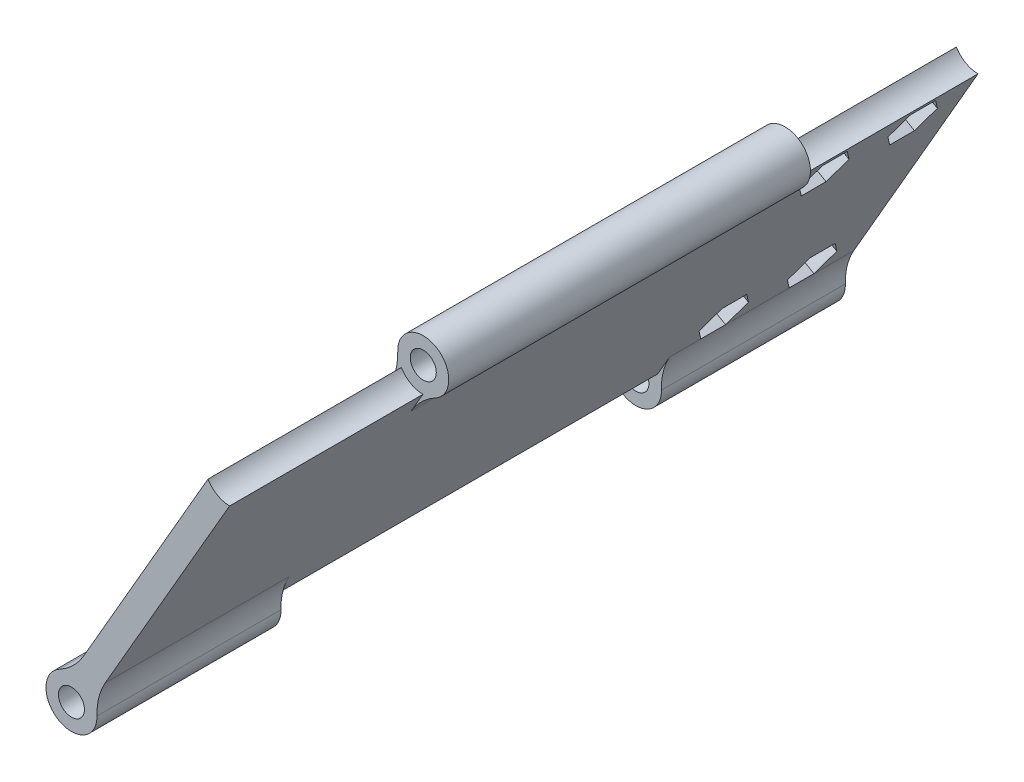
SolidWorks part; units mm, degrees
material "PLA"
ref_plane "Front Plane" through (0, 0, 0) normal (0, 0, 1) x (1, 0, 0)
ref_plane "Top Plane" through (0, 0, 0) normal (0, 1, 0) x (1, 0, 0)
ref_plane "Right Plane" through (0, 0, 0) normal (1, 0, 0) x (0, 0, -1)
sketch "Sketch2" plane through (0, 0, 0) normal (0, 0, 1) x (1, 0, 0)
  line L0 (0, 0) -> (38.1, 0)
  line L1 (0, 0) -> (0, -38.1)
  circle A0 centre (0, 0) radius 38.1
  circle A1 centre (0, -29.337) radius 1.5875
  circle A2 centre (-25.4066, 14.6685) radius 1.5875
  circle A3 centre (25.4066, 14.6685) radius 1.5875
  point P13 (0, 0)
  dimension "D1" = 76.2
  dimension "D2" = 3.175
  dimension "D3" = 8.763
  dimension "D4" = 3
extrude "Boss-Extrude1" add sketch "Sketch2" along normal blind 10 contours A1 L1 L0 A0 A3 A2 | A1 L1 A0 L0
sketch "Sketch3" plane through (0, 0, 10) normal (0, 0, 1) x (1, 0, 0)
  line L1 (0, -29.337) -> (25.4066, 14.6685)
  line L2 (1.7321, -30.337) -> (27.1386, 13.6685)
  line L3 (-1.7321, -28.337) -> (23.6745, 15.6685)
  circle A11 centre (0, -29.337) radius 1.5875
  circle A12 centre (25.4066, 14.6685) radius 1.5875
  circle A17 centre (0, -29.337) radius 2.0875
  circle A18 centre (25.4066, 14.6685) radius 2.0875
  circle A19 centre (0, -29.337) radius 4.0875
  circle A20 centre (25.4066, 14.6685) radius 4.0875
  dimension "D1" = 0.5
  dimension "D2" = 2
  dimension "D4" = 2
  dimension "D5" = 2
extrude "Boss-Extrude2" add sketch "Sketch3" along normal blind 120 separate body contours L2 A20 L3 A18 | L1 A20 L2 A18 | L3 A20 L1 A18 | A20 L1 A19 L2 | A20 L3 A19 L1 | L1 A19 L3 A17 | L2 A19 L1 A17 | L3 A19 L2 A17
delete or keep bodies "Body-Delete/Keep 2" type delete bodies bodies 101
ref_plane "Plane1" through (0, 0, 70) normal (0, 0, 1) x (1, 0, 0)
sketch "Sketch4" plane through (0, 0, 70) normal (0, 0, 1) x (1, 0, 0)
  circle A1 centre (0, -29.337) radius 4.0875
extrude "Cut-Extrude1" cut sketch "Sketch4" against normal blind 30.5 and the other way blind 30.5
sketch "Sketch5" plane through (0, 0, 10) normal (0, 0, -1) x (-1, 0, 0)
  circle A0 centre (-25.4066, 14.6685) radius 4.0875
extrude "Cut-Extrude2" cut sketch "Sketch5" against normal offset from surface (31 mm away) 1.5 up to face at (2.0875, -29.337, 39.5) offset beyond the face yes
sketch "Sketch6" plane through (0, 0, 130) normal (0, 0, 1) x (1, 0, 0)
  circle A0 centre (25.4066, 14.6685) radius 4.0875
extrude "Cut-Extrude3" cut sketch "Sketch6" against normal offset from surface (31 mm away) 1.5 contours A0 up to face at (2.0875, -29.337, 100.5) offset beyond the face yes
fillet "Fillet1" radius 10 6 edges at (21.8921, 12.5813, 70) (0.0503, -25.2498, 24.75) (0.0503, -25.2498, 115.25) (3.5144, -27.2498, 115.25) (3.5144, -27.2498, 24.75) (25.3562, 10.5813, 70)
sketch "Sketch7" plane through (10.9712, -6.3343, 0) normal (-0.866, 0.5, 0) x (0, 0, 1)
  circle A0 centre (18.3842, -14.5821) radius 1.5
  circle A1 centre (32.5542, -14.5821) radius 1.5
  circle A2 centre (18.3842, 17.6479) radius 1.5
  circle A3 centre (32.5542, 17.6479) radius 1.5
extrude "Cut-Extrude4" cut sketch "Sketch7" against normal up to surface (4 mm away) contours A0 | A2 | A3 | A1 up to face at (14.7532, -7.7836, 70)
sketch "Sketch8" plane through (14.4353, -8.3342, 0) normal (0.866, -0.5, 0) x (0, 0, -1)
  line L25 (-28.5948, 17.6686) -> (-30.5924, 21.0872)
  line L26 (-30.5924, 21.0872) -> (-34.5518, 21.0665)
  line L27 (-34.5518, 21.0665) -> (-36.5137, 17.6272)
  line L28 (-36.5137, 17.6272) -> (-34.5161, 14.2086)
  line L29 (-34.5161, 14.2086) -> (-30.5566, 14.2293)
  line L30 (-30.5566, 14.2293) -> (-28.5948, 17.6686)
  line L31 (-14.4248, 17.6686) -> (-16.4224, 21.0872)
  line L32 (-16.4224, 21.0872) -> (-20.3818, 21.0665)
  line L33 (-20.3818, 21.0665) -> (-22.3437, 17.6272)
  line L34 (-22.3437, 17.6272) -> (-20.3461, 14.2086)
  line L35 (-20.3461, 14.2086) -> (-16.3866, 14.2293)
  line L36 (-16.3866, 14.2293) -> (-14.4248, 17.6686)
  line L37 (-14.4248, -14.5614) -> (-16.4224, -11.1428)
  line L38 (-16.4224, -11.1428) -> (-20.3818, -11.1635)
  line L39 (-20.3818, -11.1635) -> (-22.3437, -14.6028)
  line L40 (-22.3437, -14.6028) -> (-20.3461, -18.0214)
  line L41 (-20.3461, -18.0214) -> (-16.3866, -18.0007)
  line L42 (-16.3866, -18.0007) -> (-14.4248, -14.5614)
  line L43 (-28.5948, -14.5614) -> (-30.5924, -11.1428)
  line L44 (-30.5924, -11.1428) -> (-34.5518, -11.1635)
  line L45 (-34.5518, -11.1635) -> (-36.5137, -14.6028)
  line L46 (-36.5137, -14.6028) -> (-34.5161, -18.0214)
  line L47 (-34.5161, -18.0214) -> (-30.5566, -18.0007)
  line L48 (-30.5566, -18.0007) -> (-28.5948, -14.5614)
  circle A0 centre (-32.5542, 17.6479) radius 3.429 construction
  circle A1 centre (-18.3842, 17.6479) radius 3.429 construction
  circle A2 centre (-18.3842, -14.5821) radius 3.429 construction
  circle A3 centre (-32.5542, -14.5821) radius 3.429 construction
  circle M4 centre (-32.5542, 17.6479) radius 1.5
  circle M5 centre (-18.3842, 17.6479) radius 1.5
  circle M6 centre (-18.3842, -14.5821) radius 1.5
  dimension "D1" = 6.858
extrude "Cut-Extrude5" cut sketch "Sketch8" against normal blind 2 contours L29 L30 L25 L26 L27 L28 M6 | L47 L48 L43 L44 L45 L46 M5 | L41 L42 L37 L38 L39 L40 M4 | L35 L36 L31 L32 L33 L34
